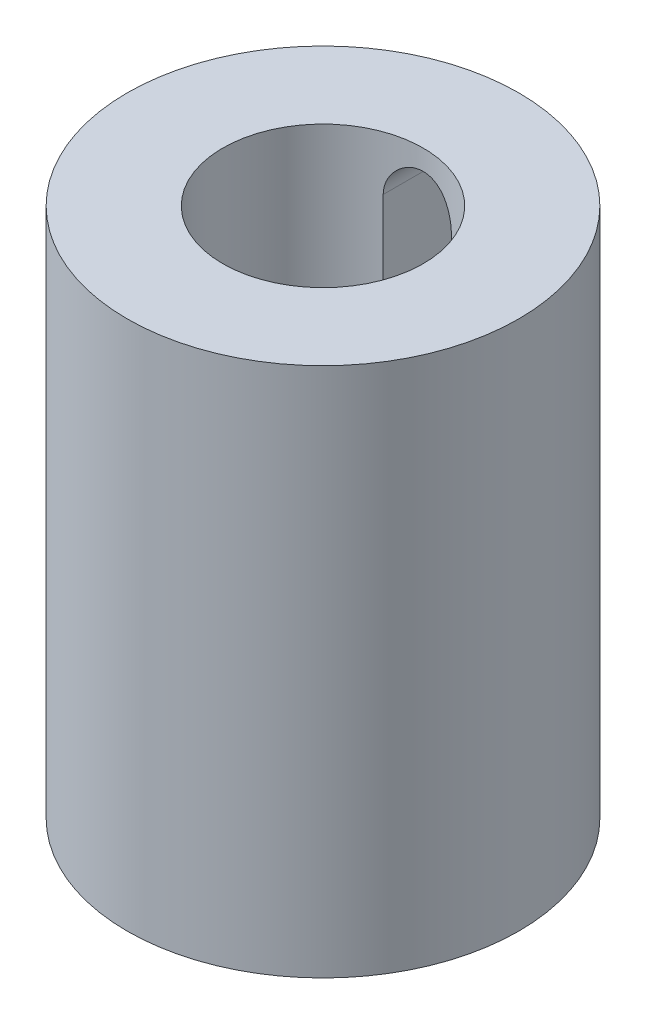
SolidWorks part; units mm, degrees
ref_plane "Front Plane" through (0, 0, 0) normal (0, 0, 1) x (1, 0, 0)
ref_plane "Top Plane" through (0, 0, 0) normal (0, 1, 0) x (1, 0, 0)
ref_plane "Right Plane" through (0, 0, 0) normal (1, 0, 0) x (0, 0, -1)
sketch "Sketch1" plane through (0, 0, 0) normal (0, 0, 1) x (1, 0, 0)
  line L0 (0, 46.0659) -> (0, -33.9341) construction
  line L2 (15.1209, 46.0659) -> (29.5385, 46.0659)
  line L3 (15.1209, 46.0659) -> (15.1209, -33.9341)
  line L4 (15.1209, -33.9341) -> (29.5385, -33.9341)
  line L5 (29.5385, 46.0659) -> (29.5385, -33.9341)
  dimension "D1" = 80
revolve "Revolve1" add sketch "Sketch1" angle 360 about L0
sketch "Sketch2" plane through (0, 0, 0) normal (0, 0, 1) x (1, 0, 0)
  line L0 (0, 37.8697) -> (0, -27.1299) construction
  line L1 (5.14, 37.8697) -> (5.14, -27.1299)
  line L2 (-5.14, 37.8697) -> (-5.14, -27.1299)
  arc A0 (5.14, 37.8697) -> (-5.14, 37.8697) centre (0, 37.8697) ccw
  arc A1 (-5.14, -27.1299) -> (5.14, -27.1299) centre (0, -27.1299) ccw
  point P3 (0, 5.3699)
extrude "Cut-Extrude1" cut sketch "Sketch2" against normal through all
